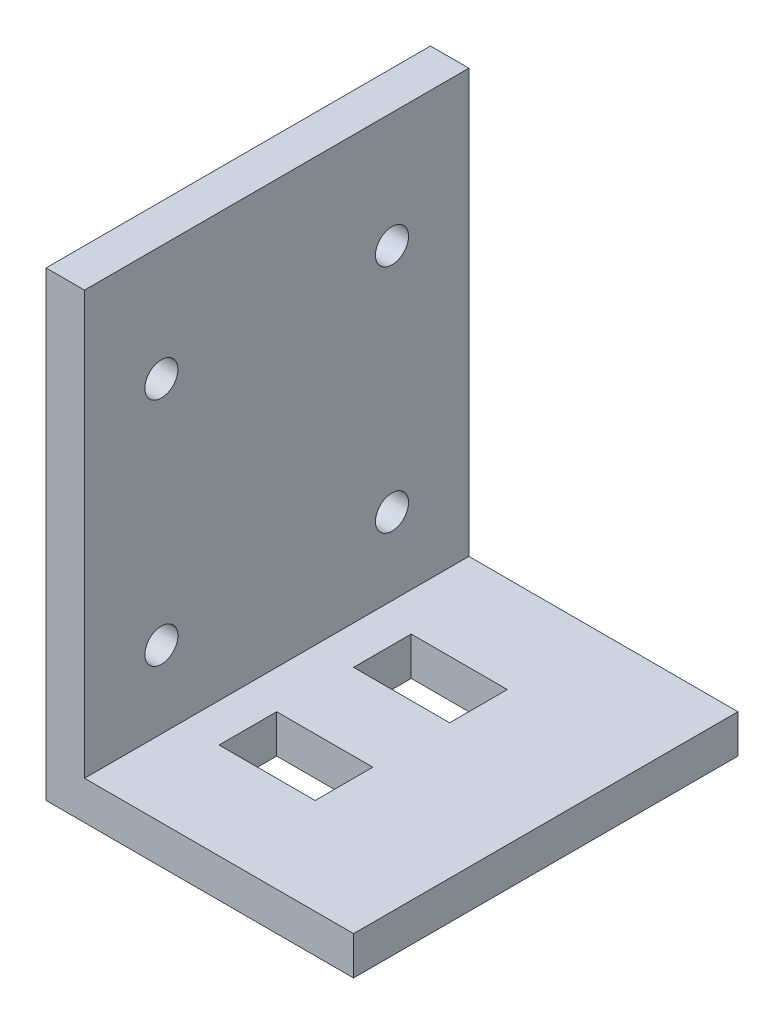
SolidWorks part; units mm, degrees
ref_plane "Front Plane" through (0, 0, 0) normal (0, 0, 1) x (1, 0, 0)
ref_plane "Top Plane" through (0, 0, 0) normal (0, 1, 0) x (1, 0, 0)
ref_plane "Right Plane" through (0, 0, 0) normal (1, 0, 0) x (0, 0, -1)
sketch "Sketch1" plane through (0, 0, 0) normal (0, 0, 1) x (1, 0, 0)
  line L1 (0, 0) -> (25.4, 0)
  line L2 (0, 0) -> (0, 38.1)
  line L3 (0, 38.1) -> (3.175, 38.1)
  line L4 (25.4, 0) -> (25.4, 3.175)
  line L7 (25.4, 3.175) -> (3.175, 3.175)
  line L8 (3.175, 38.1) -> (3.175, 3.175)
  dimension "D1" = 38.1
  dimension "D2" = 25.4
  dimension "D3" = 3.175
  dimension "D4" = 3.175
extrude "Boss-Extrude1" add sketch "Sketch1" along normal blind 31.75
sketch "Sketch2" plane through (3.175, 0, 0) normal (1, 0, 0) x (0, 0, -1)
  line L0 (-31.75, 3.175) -> (-31.75, 38.1) construction
  line L1 (-31.75, 3.175) -> (0, 3.175) construction
  circle A0 centre (-25.4, 28.575) radius 1.3667
  circle A1 centre (-6.35, 28.575) radius 1.3667
  circle A2 centre (-25.4, 9.525) radius 1.3667
  circle A3 centre (-6.35, 9.525) radius 1.3667
  dimension "D1" = 19.05
  dimension "D2" = 19.05
  dimension "D3" = 6.35
  dimension "D4" = 6.35
extrude "Cut-Extrude1" cut sketch "Sketch2" against normal through all
sketch "Sketch4" plane through (0, 3.175, 0) normal (0, 1, 0) x (1, 0, 0)
  line L0 (25.4, -15.875) -> (3.0493, -15.875) construction
  line L1 (6.35, -23.8125) -> (14.2875, -23.8125)
  line L2 (6.35, -23.8125) -> (6.35, -19.05)
  line L3 (6.35, -19.05) -> (14.2875, -19.05)
  line L4 (14.2875, -23.8125) -> (14.2875, -19.05)
  line L5 (6.35, -12.7) -> (14.2875, -12.7)
  line L6 (6.35, -12.7) -> (6.35, -7.9375)
  line L7 (6.35, -7.9375) -> (14.2875, -7.9375)
  line L8 (14.2875, -12.7) -> (14.2875, -7.9375)
  line L9 (25.4, -31.75) -> (25.4, 0) construction
  line L10 (3.175, -31.75) -> (3.175, 0) construction
  dimension "D1" = 4.7625
  dimension "D2" = 7.9375
  dimension "D3" = 6.35
  dimension "D4" = 3.175
  dimension "D5" = 3.175
extrude "Cut-Extrude2" cut sketch "Sketch4" against normal through all
